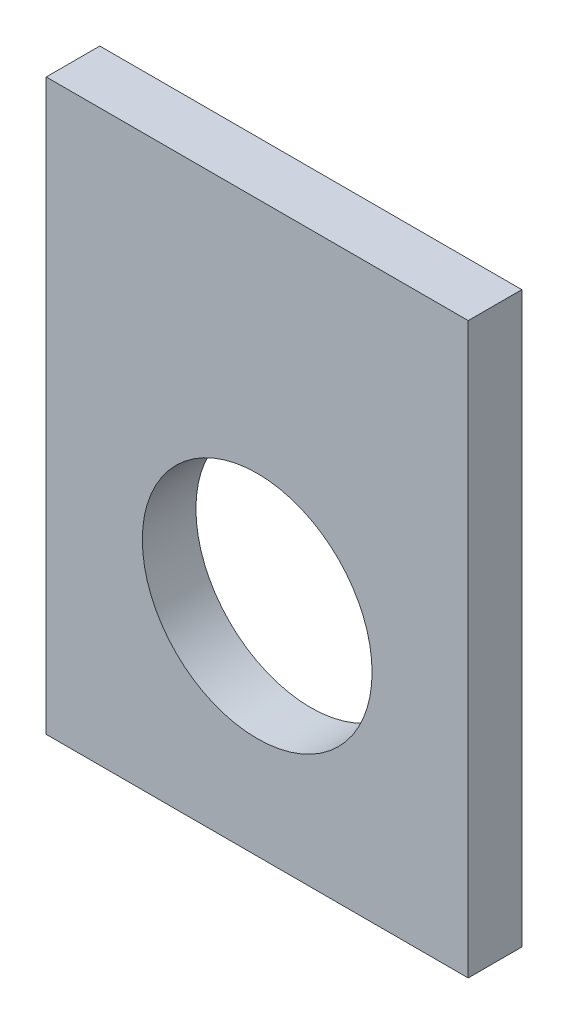
SolidWorks part; units mm, degrees
ref_plane "Front Plane" through (0, 0, 0) normal (0, 0, 1) x (1, 0, 0)
ref_plane "Top Plane" through (0, 0, 0) normal (0, 1, 0) x (1, 0, 0)
ref_plane "Right Plane" through (0, 0, 0) normal (1, 0, 0) x (0, 0, -1)
sketch "Sketch1" plane through (0, 0, 0) normal (0, 0, 1) x (1, 0, 0)
  line L5 (-12.6, 17) -> (12.6, 17)
  line L6 (-12.6, 17) -> (-12.6, -17)
  line L7 (-12.6, -17) -> (12.6, -17)
  line L8 (12.6, 17) -> (12.6, -17)
  line L9 (-12.6, 17) -> (12.6, -17) construction
  line L10 (-12.6, -17) -> (12.6, 17) construction
  dimension "D1" = 25.2
  dimension "D2" = 34
extrude "Boss-Extrude1" add sketch "Sketch1" along normal blind 3.2
sketch "Sketch4" plane through (0, 0, 3.2) normal (0, 0, 1) x (1, 0, 0)
  line L0 (12.6, 17) -> (-12.6, 17) construction
  circle A0 centre (0, -4.06) radius 6.86
  dimension "D1" = 13.72
  dimension "D2" = 21.06
extrude "Cut-Extrude1" cut sketch "Sketch4" against normal up to next
